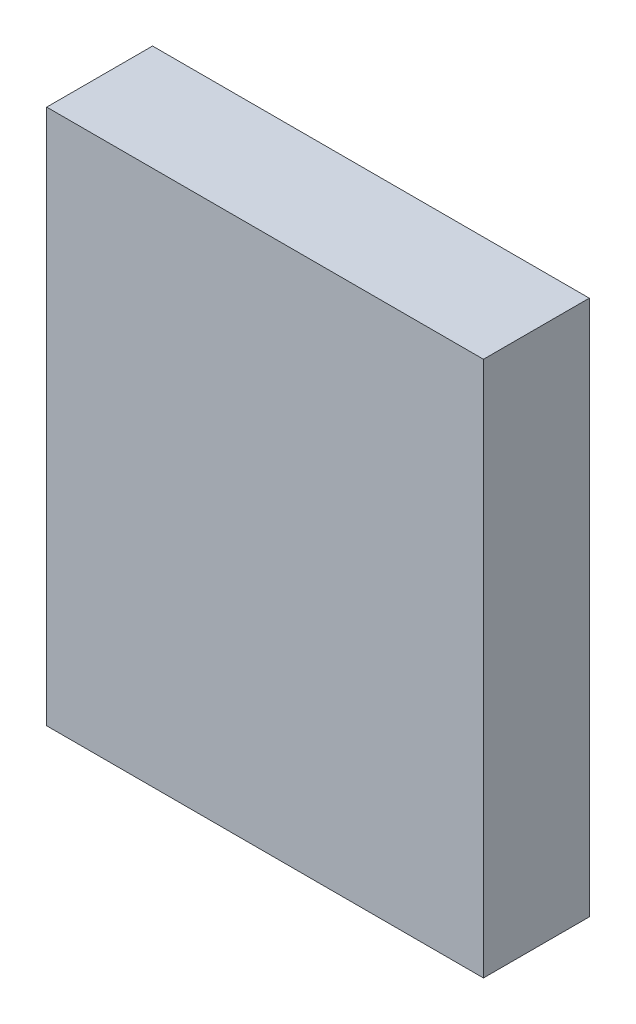
SolidWorks part; units mm, degrees
ref_plane "Front Plane" through (0, 0, 0) normal (0, 0, 1) x (1, 0, 0)
ref_plane "Top Plane" through (0, 0, 0) normal (0, 1, 0) x (1, 0, 0)
ref_plane "Right Plane" through (0, 0, 0) normal (1, 0, 0) x (0, 0, -1)
sketch "Sketch1" plane through (0, 0, 0) normal (0, 0, 1) x (1, 0, 0)
  line L0 (-2.0635, 2.5635) -> (2.0635, 2.5635)
  line L1 (2.0635, 2.5635) -> (2.0635, -2.5)
  line L2 (2.0635, -2.5) -> (-2.0635, -2.5)
  line L3 (-2.0635, -2.5) -> (-2.0635, 2.5635)
extrude "Component_Outline" add sketch "Sketch1" along normal blind 1 separate body
sketch3d "3DSketch1"
  line L0 (0, 0, 0) -> (1, 0, 0)
  line L1 (0, 0, 0) -> (0, 1, 0)
  line L2 (0, 0, 0) -> (0, 0, 1)
  point P0 (0, 0, 0)
